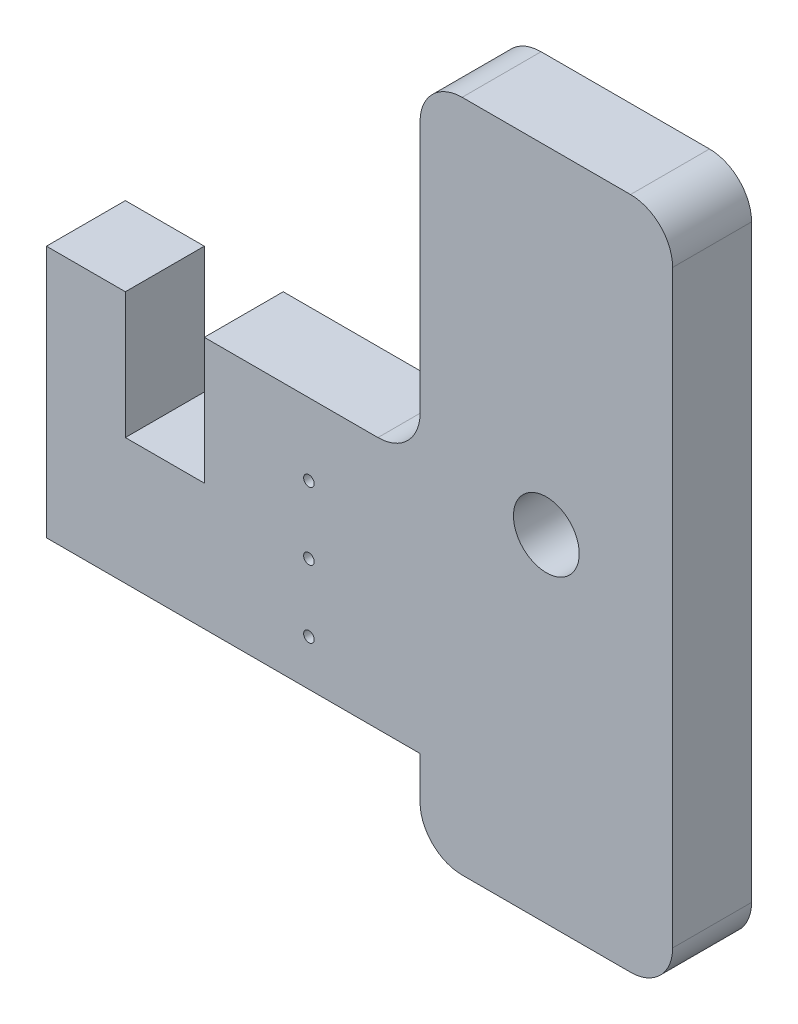
SolidWorks part; units mm, degrees
ref_plane "Front Plane" through (0, 0, 0) normal (0, 0, 1) x (1, 0, 0)
ref_plane "Top Plane" through (0, 0, 0) normal (0, 1, 0) x (1, 0, 0)
ref_plane "Right Plane" through (0, 0, 0) normal (1, 0, 0) x (0, 0, -1)
sketch "Sketch1" plane through (0, 0, 0) normal (0, 0, 1) x (1, 0, 0)
  line L0 (0, 38.1) -> (0, -38.1) construction
  line L2 (-15.24, -40.64) -> (15.24, -40.64)
  line L3 (-15.24, -40.64) -> (-15.24, 40.64) construction
  line L4 (-15.24, 40.64) -> (15.24, 40.64)
  line L5 (15.24, -40.64) -> (15.24, 40.64)
  line L6 (-15.24, -40.64) -> (15.24, 40.64) construction
  line L7 (-15.24, 40.64) -> (15.24, -40.64) construction
  line L10 (-15.24, 15.24) -> (15.24, 15.24) construction
  line L12 (-15.24, -15.24) -> (15.24, -15.24) construction
  line L20 (-15.24, -40.64) -> (-15.24, -30.48)
  line L21 (-15.24, 40.64) -> (-15.24, 0)
  line L22 (-15.24, -30.48) -> (-60.325, -30.48) construction
  line L23 (-15.24, 0) -> (-60.325, 0) construction
  line L24 (-60.325, 0) -> (-60.325, -30.48)
  line L25 (-15.24, -15.24) -> (-60.325, -15.24) construction
  line L26 (-41.275, 0) -> (-41.275, -30.48) construction
  line L27 (-60.325, -30.48) -> (-50.8, -30.48) construction
  line L28 (-50.8, -30.48) -> (-41.275, -30.48) construction
  line L29 (-50.8, -30.48) -> (-50.8, -15.24) construction
  line L30 (-50.8, -15.24) -> (-41.275, -15.24) construction
  line L31 (-41.275, -30.48) -> (-41.275, -15.24) construction
  line L32 (-50.8, -30.48) -> (-41.275, -15.24) construction
  line L33 (-50.8, -15.24) -> (-41.275, -30.48) construction
  line L34 (-41.275, -30.48) -> (-15.24, -30.48) construction
  line L35 (-60.325, -30.48) -> (-15.24, -30.48)
  line L36 (-60.325, 0) -> (-50.8, 0)
  line L37 (-50.8, -15.24) -> (-41.275, -15.24)
  line L38 (-50.8, -15.24) -> (-50.8, 0)
  line L39 (-50.8, 0) -> (-41.275, 0) construction
  line L40 (-41.275, -15.24) -> (-41.275, 0)
  line L41 (-41.275, 0) -> (-15.24, 0)
  circle A7 centre (0, 0) radius 3.9688
  circle A8 centre (0, 0) radius 38.1 construction
  circle A9 centre (0, 0) radius 15.24 construction
  circle A16 centre (0, 0) radius 40.64 construction
  circle A17 centre (0, 0) radius 41.275 construction
  point P21 (-46.0375, -22.86)
  dimension "D1" = 7.9375
  dimension "D4" = 2.54
  dimension "D6" = 9.525
  dimension "D7" = 9.525
  dimension "D8" = 3.175
  dimension "D2" = 76.2
  dimension "D3" = 30.48
  dimension "D5" = 10.16
extrude "Boss-Extrude1" add sketch "Sketch1" along normal blind 9.525 contours L31 L34 L20 L2 L5 L4 L21 L23 L24 L27 L29 L30 A7
fillet "Fillet2" radius 5.08 5 edges at (-15.24, -40.64, 4.7625) (-15.24, 40.64, 4.7625) (15.24, 40.64, 4.7625) (15.24, -40.64, 4.7625) (-15.24, 0, 4.7625)
sketch "Sketch2" plane through (0, 0, 9.525) normal (0, 0, 1) x (1, 0, 0)
  circle A0 centre (-28.6512, -8.683) radius 0.635
  circle A1 centre (-28.6512, -16.8255) radius 0.635
  circle A2 centre (-28.6512, -24.9681) radius 0.635
  dimension "D1" = 1.27
extrude "Cut-Extrude1" cut sketch "Sketch2" against normal up to next
